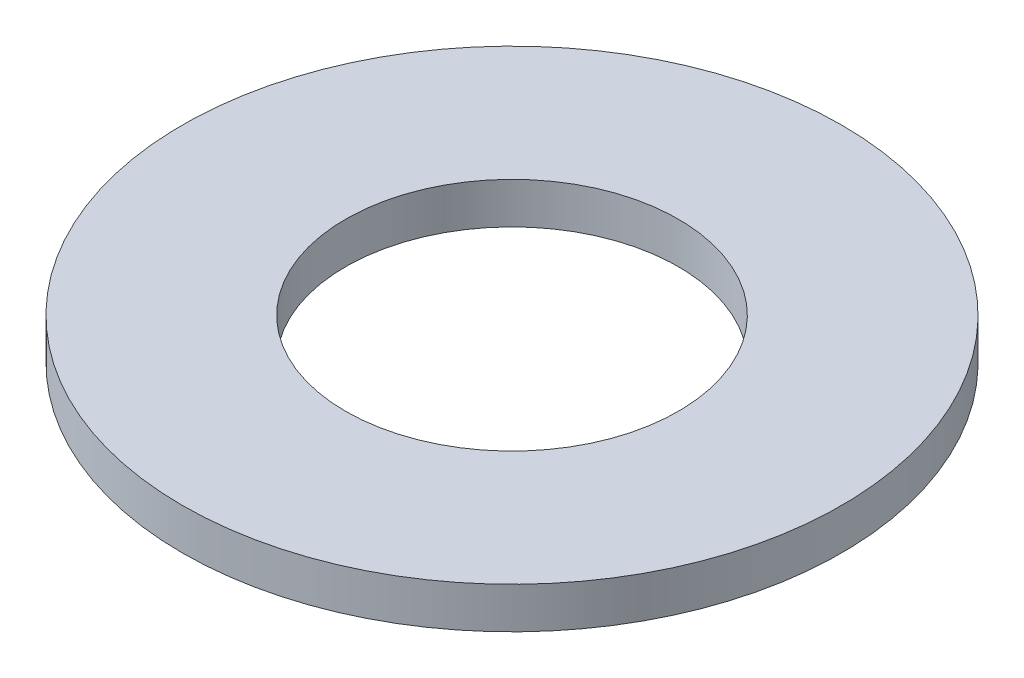
SolidWorks part; units mm, degrees
material "Alum Plate"
ref_plane "Front Plane" through (0, 0, 0) normal (0, 0, 1) x (1, 0, 0)
ref_plane "Top Plane" through (0, 0, 0) normal (0, 1, 0) x (1, 0, 0)
ref_plane "Right Plane" through (0, 0, 0) normal (1, 0, 0) x (0, 0, -1)
other "Bounding Box"
ref_plane "Default Plane" through (-8.9266, -12.7485, 0) normal (-0.1736, 0.9848, 0) x (0.9848, 0.1736, 0)
sketch "Sketch1" plane through (0, 0, 0) normal (0, 1, 0) x (1, 0, 0)
  circle A0 centre (0, 0) radius 6.4135
  circle A1 centre (0, 0) radius 12.7
  dimension "D1" = 12.827
  dimension "D2" = 25.4
extrude "Boss-Extrude1" add sketch "Sketch1" along normal mid plane 1.5875
